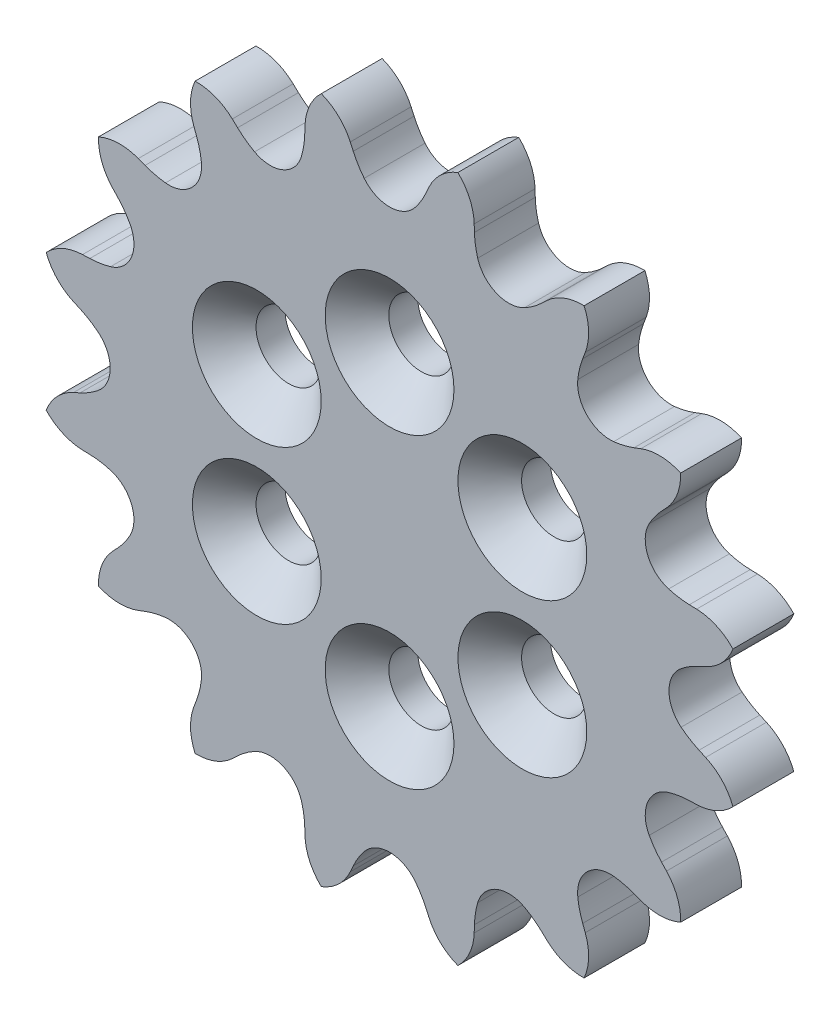
SolidWorks part; units mm, degrees
material "6061-T6 (SS)"
ref_plane "Front" through (0, 0, 0) normal (0, 0, 1) x (1, 0, 0)
ref_plane "Top" through (0, 0, 0) normal (0, 1, 0) x (1, 0, 0)
ref_plane "Right" through (0, 0, 0) normal (1, 0, 0) x (0, 0, -1)
sketch "Sketch1" plane through (0, 0, 0) normal (0, 0, 1) x (1, 0, 0)
  line L0 (-22.1739, 16.2745) -> (32.5988, 16.2745) construction
  line L1 (0, 43.7023) -> (0, 0) construction
  line L2 (2.0601, 40.8654) -> (2.0601, 26.2717) construction
  line L3 (-5.4717, 17.928) -> (10.2042, 17.928) construction
  line L4 (2.0601, 17.928) -> (-3.2103, 13.698) construction
  line L5 (2.0601, 17.928) -> (-1.896, 16.1459) construction
  line L6 (-1.896, 16.1459) -> (-2.0514, 16.491)
  line L7 (-4.534, 37.4786) -> (-4.534, 25.9898) construction
  line L8 (6.0239, 15.3726) -> (-6.287, 15.3726) construction
  line L9 (0, 0) -> (-7.6397, 38.4072) construction
  circle A2 centre (0, 0) radius 16.2745 construction
  arc A5 (-1.6969, 16.2355) -> (-1.6974, 16.2745) centre (0, 16.2745) ccw
  arc A6 (-1.3237, 15.2121) -> (-1.896, 16.1459) centre (2.0601, 17.928) cw
  arc A8 (-1.3237, 15.2121) -> (0, 14.5772) centre (0, 16.2745) ccw
  arc A9 (-2.0514, 16.491) -> (-4.534, 18.0955) centre (-4.534, 15.3726) ccw
  dimension "D1" = 32.549
  dimension "D2" = 1.6974
  dimension "D8" = 4.339
  dimension "D3" = 1.6534
  dimension "D4" = 2.0601
  dimension "D5" = 38.75
  dimension "D6" = 14.5
  dimension "D7" = 4.339
  dimension "D9" = 4.534
  dimension "D10" = 0.9019
  dimension "D12" = 11.25
sketch "Sketch3" plane through (0, 0, 0) normal (0, 0, 1) x (1, 0, 0)
  circle A0 centre (0, 0) radius 18.6548
extrude "Boss-Extrude1" add sketch "Sketch3" along normal blind 3.175
sketch "Sketch2" plane through (0, 0, 0) normal (0, 0, 1) x (1, 0, 0)
  line L0 (-1.896, 16.1459) -> (-2.0514, 16.491) construction
  line L1 (-1.896, 16.1459) -> (-2.0514, 16.491)
  line L2 (0, 14.5772) -> (0, 34.1669) construction
  line L3 (0, 43.7023) -> (0, 0) construction
  line L4 (1.896, 16.1459) -> (2.0514, 16.491)
  arc A0 (-1.3237, 15.2121) -> (0, 14.5772) centre (0, 16.2745) ccw construction
  arc A1 (-1.896, 16.1459) -> (-1.3237, 15.2121) centre (2.0601, 17.928) ccw construction
  arc A2 (-2.0514, 16.491) -> (-4.534, 18.0955) centre (-4.534, 15.3726) ccw construction
  arc A3 (-1.3237, 15.2121) -> (1.3237, 15.2121) centre (0, 16.2745) ccw
  arc A4 (-1.896, 16.1459) -> (-1.3237, 15.2121) centre (2.0601, 17.928) ccw
  arc A5 (-2.0514, 16.491) -> (-4.534, 18.0955) centre (-4.534, 15.3726) ccw
  arc A6 (2.0514, 16.491) -> (4.534, 18.0955) centre (4.534, 15.3726) cw
  arc A7 (1.896, 16.1459) -> (1.3237, 15.2121) centre (-2.0601, 17.928) cw
extrude "Cut-Extrude1" cut sketch "Sketch2" against normal through all and the other way through all flip side to cut
ref_axis "Axis1" through (0, 0, -80.9) along (0, 0, 1)
pattern_circular "CirPattern1" count 16 over 360 about axis through (0, 0, -80.9) along (0, 0, 1) of "Cut-Extrude1"
sketch "Sketch6" plane through (0, 0, 3.175) normal (0, 0, 1) x (1, 0, 0)
  circle A0 centre (0, 0) radius 8 construction
  point P0 (0, 8)
  point P12 (6.9282, 4)
  point P13 (6.9282, -4)
  point P14 (0, -8)
  point P15 (-6.9282, -4)
  point P16 (-6.9282, 4)
  point P18 (7.4895, 2.8119)
  point P19 (0, 0)
  dimension "D1" = 16
  dimension "D2" = 6
hole_wizard "CSK for M3 SFHCS1" positions "Sketch6" profile "Sketch5" countersink size "M3" standard "ANSI Metric" end condition through all
sketch "Sketch5" plane through (0, 8, 3.175) normal (1, 0, 0) x (0, -1, 0)
  line L0 (0, 0) -> (0, 3.175)
  line L1 (0, 3.175) -> (1.7, 3.175)
  line L2 (1.7, 3.175) -> (1.7, 1.66)
  line L3 (1.7, 1.66) -> (3.36, 0)
  line L5 (3.36, 0) -> (0, 0)
  line L6 (-1.7, 1.66) -> (-3.36, 0) construction
  line L11 (0, -6.35) -> (0, 107.95) construction
  dimension "Thru Hole Dia." = 3.4
  dimension "Thru Hole Depth" = 3.175
  dimension "Near C'Sink Dia." = 6.72
  dimension "Near C'Sink Angle" = 90
equation "\"P\"= iif ( \"P1\" = 25 , .25 , iif ( \"P1\" = 35 , .375 , .5 ) )'Chain Pitch"
equation "\"N\"= \"N0\"'Number of Teeth"
equation "\"Dr\"= iif ( \"P1\" = 25 , .13 , .2 )'Roller Diameter"
equation "\"Ds\"= 1.005 * \"Dr\" + .003"
equation "\"R\"= \"Ds\" / 2"
equation "\"A\"= 35 + ( 60 / \"N\" )"
equation "\"B\"= 18 - ( 56 / \"N\" )"
equation "\"ac\"= .8 * \"Dr\""
equation "\"M\"= .8 * \"Dr\" * cos ( 35 + ( 60 / \"N\" ) )"
equation "\"T\"= abs ( .8 * \"Dr\" * sin ( 35 + ( 60 / \"N\" ) ) )"
equation "\"E\"= 1.3025 * \"Dr\" + .0015"
equation "\"yz\"= \"Dr\" * ( 1.4 * sin ( 17 - ( 64 / \"N\" ) ) - .8 * sin ( 18 - ( 56 / \"N\" ) ) )"
equation "\"ab\"= 1.4 * \"Dr\""
equation "\"W\"= 1.4 * \"Dr\" * cos ( 180 / \"N\" )"
equation "\"V\"= abs ( 1.4 * \"Dr\" * sin ( 180 / \"N\" ) )"
equation "\"F\"= abs ( \"Dr\" * ( .8 * cos ( 18 - ( 56 / \"N\" ) ) + 1.4 * cos ( 17 - ( 64 / \"N\" ) ) - 1.3025 ) - .0015 )"
equation "\"PD\"= \"P\" / sin ( 180 / \"N\" )'Pitch Diamerter"
equation "\"D3@Sketch1\"=\"T\""
equation "\"D8@Sketch1\"=\"E\""
equation "\"D1@Sketch1\"=\"PD\""
equation "\"D4@Sketch1\"=\"M\""
equation "\"D5@Sketch1\"=\"A\""
equation "\"D6@Sketch1\"=\"B\""
equation "\"D7@Sketch1\"=\"E\""
equation "\"D9@Sketch1\"=\"W\""
equation "\"D10@Sketch1\"=\"V\""
equation "\"D12@Sketch1\"=180/\"N\""
equation "\"D1@CirPattern1\"=\"N\""
equation "\"D2@Sketch1\"=\"R\""
equation "\"P1\"= \"P0\""
equation "\"Thk\"= iif ( \"P1\" = 25 , .125 , .1875 )'Plate Thickness"
equation "\"D1@Boss-Extrude1\"=\"Thk\""
